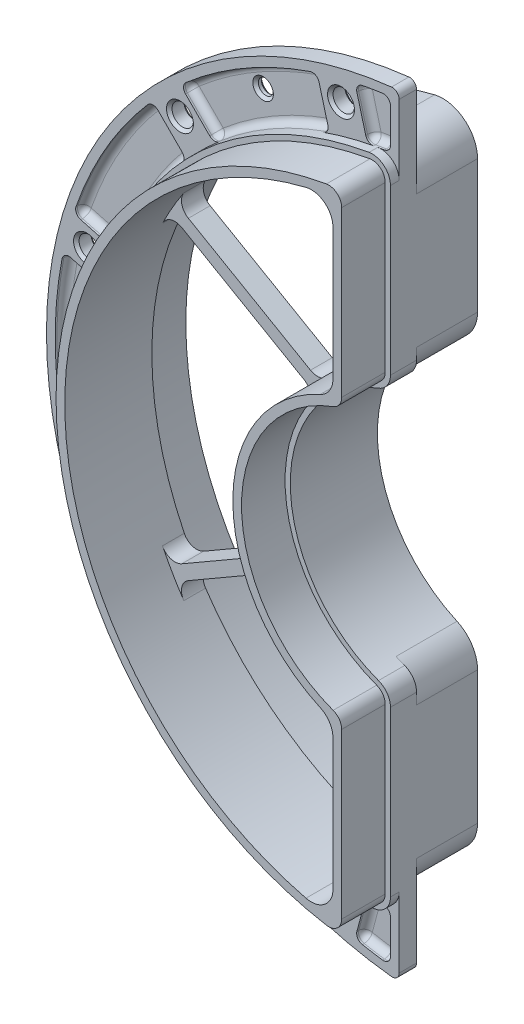
SolidWorks part; units mm, degrees
material "6061 Alloy"
ref_plane "Front" through (0, 0, 0) normal (0, 0, 1) x (1, 0, 0)
ref_plane "Top" through (0, 0, 0) normal (0, 1, 0) x (1, 0, 0)
ref_plane "Right" through (0, 0, 0) normal (1, 0, 0) x (0, 0, -1)
sketch "Sketch1" plane through (0, 0, 0) normal (0, 0, 1) x (1, 0, 0)
  line L0 (-8, 75.5778) -> (-8, 29.95)
  line L1 (0, 0) -> (0, 48.8788) construction
  line L2 (-8, -29.95) -> (-8, -75.5778)
  line L3 (0, 0) -> (58.2509, 0) construction
  arc A0 (-8, 75.5778) -> (-8, -75.5778) centre (0, 0) ccw
  arc A1 (-8, 29.95) -> (-8, -29.95) centre (0, 0) ccw
  dimension "D1" = 76
  dimension "D2" = 31
  dimension "D3" = 8
extrude "Extrude-Thin1" add sketch "Sketch1" along normal blind 16 thin
fillet "Fillet1" radius 5 4 edges at (-11.2, -71.9333, 8) (-11.2, -32.3141, 8) (-11.2, 32.3141, 8) (-11.2, 71.9333, 8)
fillet "Fillet2" radius 4.2 4 edges at (-8, 75.5778, 8) (-8, 29.95, 8) (-8, -29.95, 8) (-8, -75.5778, 8)
sketch "Sketch2" plane through (0, 0, 16) normal (0, 0, 1) x (1, 0, 0)
  line L0 (-8, 33.0182) -> (-8, 70.7559) construction
  line L1 (-8, -70.7559) -> (-8, -33.0182) construction
  line L2 (-8, 33.0182) -> (-8, 70.7559)
  line L3 (-8, -70.7559) -> (-8, -33.0182)
  arc A0 (-8, 70.7559) -> (-12.9136, 74.8948) centre (-12.2, 70.7559) ccw construction
  arc A1 (-12.9136, 74.8948) -> (-12.9136, -74.8948) centre (0, 0) ccw construction
  arc A2 (-12.9136, -74.8948) -> (-8, -70.7559) centre (-12.2, -70.7559) ccw construction
  arc A3 (-8, -33.0182) -> (-10.7443, -29.0785) centre (-12.2, -33.0182) ccw construction
  arc A4 (-10.7443, 29.0785) -> (-10.7443, -29.0785) centre (0, 0) ccw construction
  arc A5 (-10.7443, 29.0785) -> (-8, 33.0182) centre (-12.2, 33.0182) ccw construction
  arc A6 (-8, 70.7559) -> (-12.9136, 74.8948) centre (-12.2, 70.7559) ccw
  arc A7 (-12.9136, 74.8948) -> (-12.9136, -74.8948) centre (0, 0) ccw
  arc A8 (-12.9136, -74.8948) -> (-8, -70.7559) centre (-12.2, -70.7559) ccw
  arc A9 (-8, -33.0182) -> (-10.7443, -29.0785) centre (-12.2, -33.0182) ccw
  arc A10 (-10.7443, 29.0785) -> (-10.7443, -29.0785) centre (0, 0) ccw
  arc A11 (-10.7443, 29.0785) -> (-8, 33.0182) centre (-12.2, 33.0182) ccw
extrude "Cut-Extrude-Thin1" cut sketch "Sketch2" against normal blind 10 thin thin type one direction reverse wall 1.2
sketch "Sketch3" plane through (0, 0, 6) normal (0, 0, 1) x (1, 0, 0)
  line L0 (0, 0) -> (-22.1291, 0) construction
  line L4 (0, 0) -> (0, 34.7436) construction
  line L5 (-8, -70.7559) -> (-8, -33.0182) construction
  line L6 (-8, -70.7559) -> (-8, -88.6397)
  line L7 (-8, 70.7559) -> (-8, 88.6397)
  arc A0 (-8, 88.6397) -> (-8, -88.6397) centre (0, 0) ccw
  arc A1 (-12.9136, 74.8948) -> (-12.9136, -74.8948) centre (0, 0) ccw construction
  arc A2 (-8, 70.7559) -> (-12.9136, 74.8948) centre (-12.2, 70.7559) ccw construction
  arc A3 (-12.9136, -74.8948) -> (-8, -70.7559) centre (-12.2, -70.7559) ccw construction
  arc A4 (-12.9136, 74.8948) -> (-12.9136, -74.8948) centre (0, 0) ccw
  arc A5 (-8, 70.7559) -> (-12.9136, 74.8948) centre (-12.2, 70.7559) ccw
  arc A6 (-12.9136, -74.8948) -> (-8, -70.7559) centre (-12.2, -70.7559) ccw
  point P10 (-138.2875, 0)
  dimension "D3" = 178
extrude "Boss-Extrude1" add sketch "Sketch3" against normal blind 4 from offset 2 separate body offset against normal yes
sketch "Sketch9" plane through (0, 0, 4) normal (0, 0, 1) x (1, 0, 0)
  line L2 (-10, 70.7559) -> (-10, 88.6397)
  line L3 (-10, 75.3392) -> (-10, 86.4234)
  line L6 (-10, -88.6397) -> (-10, -70.7559)
  line L7 (-10, -86.4234) -> (-10, -75.3392)
  arc A2 (-12.9136, 74.8948) -> (-12.9136, -74.8948) centre (0, 0) ccw construction
  arc A3 (-7.8202, 86.6478) -> (-7.8202, -86.6478) centre (0, 0) ccw
  arc A4 (-10, 86.4234) -> (-10, -86.4234) centre (0, 0) ccw
  arc A5 (-10, 75.3392) -> (-10, -75.3392) centre (0, 0) ccw
  dimension "D1" = 2
  dimension "D2" = 2
  dimension "D3" = 2
extrude "Cut-Extrude2" cut sketch "Sketch9" against normal offset from surface (2 mm away) 2 up to face at (-33.3314, 0, 0)
sketch "Sketch10" plane through (0, 0, 4) normal (0, 0, 1) x (1, 0, 0)
  line L0 (0, 0) -> (-21.0938, -78.723) construction
  line L1 (-27.058, -83.5953) -> (-18.3647, -85.9247)
  line L2 (-18.3647, -85.9247) -> (-15.1295, -73.8506)
  line L3 (-15.1295, -73.8506) -> (-23.8228, -71.5212)
  line L4 (-23.8228, -71.5212) -> (-27.058, -83.5953)
  line L5 (-18.3647, -85.9247) -> (-23.8228, -71.5212) construction
  line L6 (0, 0) -> (0, -132.8188) construction
  point P5 (-21.0938, -78.723)
  dimension "D2" = 12.5
  dimension "D1" = 81.5
  dimension "D3" = 9
  dimension "D4" = 15
extrude "Boss-Extrude2" add sketch "Sketch10" against normal up to surface (2 mm away) up to face at (-34.3197, 0, 2)
pattern_circular "CirPattern1" count 6 over 150 about axis through (0, 0, 0) along (0, 0, 1) of "Boss-Extrude2"
sketch "Sketch11" plane through (0, 0, 4) normal (0, 0, 1) x (1, 0, 0)
  line L0 (0, 0) -> (0, -70.2998) construction
  line L1 (0, 0) -> (-21.3526, -79.6889) construction
  line L2 (0, 0) -> (-58.3363, -58.3363) construction
  point P4 (-21.3526, -79.6889)
  point P8 (-58.3363, -58.3363)
  point P9 (-79.6889, -21.3526)
  point P10 (-79.6889, 21.3526)
  point P11 (-58.3363, 58.3363)
  point P12 (-21.3526, 79.6889)
  dimension "D2" = 30
  dimension "D3" = 15
  dimension "D4" = 82.5
  dimension "D1" = 6
hole_wizard "#8 Clearance Hole1" positions "3DSketch1" profile "Sketch12" hole size "#8" standard "Ansi Inch" end condition through all
sketch3d "3DSketch1"
  point P0 (-21.3526, -79.6889, 4)
  point P3 (-58.3363, -58.3363, 4)
  point P6 (-79.6889, -21.3526, 4)
  point P9 (-79.6889, 21.3526, 4)
  point P12 (-58.3363, 58.3363, 4)
  point P15 (-21.3526, 79.6889, 4)
sketch "Sketch12" plane through (-21.3526, -79.6889, 4) normal (1, 0, 0) x (0, -1, 0)
  line L0 (0, 0) -> (0, 4)
  line L1 (0, 4) -> (3.0924, 4)
  line L2 (2.4574, 3.365) -> (2.4574, 0.635)
  line L3 (2.4574, 0.635) -> (3.0924, 0)
  line L5 (3.0924, 0) -> (0, 0)
  line L6 (-2.4574, 0.635) -> (-3.0924, 0) construction
  line L7 (3.0924, 4) -> (2.4574, 3.365)
  line L8 (-3.0925, 4) -> (-2.4574, 3.365) construction
  line L11 (0, -6.35) -> (0, 107.95) construction
  dimension "Thru Hole Dia." = 4.9149
  dimension "Thru Hole Depth" = 4
  dimension "Near C'Sink Dia." = 6.1849
  dimension "Near C'Sink Angle" = 90
  dimension "Far C'Sink Dia." = 6.1849
  dimension "Far C'Sink Angle" = 90
fillet "Fillet3" radius 1.5875 56 edges at (-10, -80.8813, 2) (-14.0861, -85.8521, 2) (-16.7148, -79.767, 2) (-12.6524, -74.9394, 2) (-10, -86.4234, 3) (-10, -75.3392, 3) (-18.1404, -85.0877, 3) (-15.2891, -74.4463, 3) (-14.0861, 85.8521, 2) (-10, 80.8813, 2) (-12.6524, 74.9394, 2) (-16.7148, 79.767, 2) (-38, 65.8179, 2) (-54.3589, 60.7229, 2) (-43.5, 75.3442, 2) (-25.4081, 77.4376, 2) (-65.8179, 38, 2) (-77.4376, 25.4081, 2) (-75.3442, 43.5, 2) (-60.7229, 54.3589, 2) (-76, 0, 2) (-79.767, -16.7148, 2) (-87, 0, 2) (-79.767, 16.7148, 2) (-65.8179, -38, 2) (-60.7229, -54.3589, 2) (-75.3442, -43.5, 2) (-77.4376, -25.4081, 2) (-38, -65.8179, 2) (-25.4081, -77.4376, 2) (-43.5, -75.3442, 2) (-54.3589, -60.7229, 2) (-18.1404, 85.0877, 3) (-10, 86.4234, 3) (-15.2891, 74.4463, 3) (-10, 75.3392, 3) (-26.8338, 82.7584, 3) (-23.9824, 72.1169, 3) (-58.254, 64.6179, 3) (-50.4638, 56.8278, 3) (-82.7584, 26.8338, 3) (-64.6179, 58.254, 3) (-56.8278, 50.4638, 3) (-72.1169, 23.9824, 3) (-85.0877, 18.1404, 3) (-74.4463, 15.2891, 3) (-85.0877, -18.1404, 3) (-74.4463, -15.2891, 3) (-82.7584, -26.8338, 3) (-72.1169, -23.9824, 3) (-56.8278, -50.4638, 3) (-64.6179, -58.254, 3) (-50.4638, -56.8278, 3) (-58.254, -64.6179, 3) (-26.8338, -82.7584, 3) (-23.9824, -72.1169, 3)
fillet "Fillet4" radius 1.5875 2 edges at (-8, -88.6397, 2) (-8, 88.6397, 2)
sketch "Sketch8" plane through (0, 0, 0) normal (0, 1, 0) x (1, 0, 0)
  line L1 (-129.2875, -26.448) -> (-129.2875, -58.4649)
sketch "Sketch17" plane through (0, 0, 0) normal (0, 0, -1) x (-1, 0, 0)
  line L0 (8, 75.5778) -> (8, 29.95) construction
  line L1 (8, -29.95) -> (8, -75.5778) construction
  line L2 (8, 75.5778) -> (8, 29.95)
  line L3 (8, -29.95) -> (8, -75.5778)
  arc A0 (8, -29.95) -> (8, 29.95) centre (0, 0) ccw construction
  arc A1 (8, -75.5778) -> (8, 75.5778) centre (0, 0) ccw construction
  arc A2 (8, -29.95) -> (8, 29.95) centre (0, 0) ccw
  arc A3 (8, -75.5778) -> (8, 75.5778) centre (0, 0) ccw
extrude "Extrude-Thin2" add sketch "Sketch17" along normal blind 14 separate body thin thin type one direction reverse wall 3.2
fillet "Fillet5" radius 5 4 edges at (-11.2, 71.9333, -7) (-11.2, -71.9333, -7) (-11.2, -32.3141, -7) (-11.2, 32.3141, -7)
fillet "Fillet6" radius 8 4 edges at (-8, 29.95, -7) (-8, -29.95, -7) (-8, -75.5778, -7) (-8, 75.5778, -7)
combine bodies "Combine1" operation type add bodies to combine 113 117
sketch "Sketch7" plane through (0, 0, -14) normal (0, 0, -1) x (-1, 0, 0)
  line L4 (9, 66.0908) -> (9, 35.5668)
  line L5 (9, -35.5668) -> (9, -66.0908)
  line L6 (9, 66.0908) -> (9, 35.5668)
  line L7 (9, -35.5668) -> (9, -66.0908)
  arc A12 (17.6471, 72.8943) -> (9, 66.0908) centre (16, 66.0908) ccw
  arc A13 (9, 35.5668) -> (13.1282, 29.183) centre (16, 35.5668) ccw
  arc A14 (13.1282, -29.183) -> (13.1282, 29.183) centre (0, 0) ccw
  arc A15 (13.1282, -29.183) -> (9, -35.5668) centre (16, -35.5668) ccw
  arc A16 (9, -66.0908) -> (17.6471, -72.8943) centre (16, -66.0908) ccw
  arc A17 (17.6471, -72.8943) -> (17.6471, 72.8943) centre (0, 0) ccw
  arc A18 (17.6471, 72.8943) -> (9, 66.0908) centre (16, 66.0908) ccw
  arc A19 (9, 35.5668) -> (13.1282, 29.183) centre (16, 35.5668) ccw
  arc A20 (13.1282, -29.183) -> (13.1282, 29.183) centre (0, 0) ccw
  arc A21 (13.1282, -29.183) -> (9, -35.5668) centre (16, -35.5668) ccw
  arc A22 (9, -66.0908) -> (17.6471, -72.8943) centre (16, -66.0908) ccw
  arc A23 (17.6471, -72.8943) -> (17.6471, 72.8943) centre (0, 0) ccw
  dimension "D1" = 1
extrude "Cut-Extrude1" cut sketch "Sketch7" against normal blind 10
sketch "Sketch13" plane through (0, 0, 2) normal (0, 0, 1) x (1, 0, 0)
  line L0 (0, 0) -> (0, -89.236) construction
  line L1 (0, -89.236) -> (0, 0) construction
  line L2 (0, 0) -> (-41.25, -71.4471) construction
  dimension "D1" = 30
  dimension "D2" = 82.5
hole_wizard "#29 (0.136) Diameter Hole1" positions "Sketch15" profile "Sketch14" hole size "#29" standard "Ansi Inch" end condition up to next
sketch "Sketch15" plane through (0, 0, 2) normal (0, 0, 1) x (1, 0, 0)
  point P0 (-41.25, -71.4471)
sketch "Sketch14" plane through (-41.25, -71.4471, 2) normal (1, 0, 0) x (0, -1, 0)
  line L0 (0, 0) -> (0, 2)
  line L1 (0, 2) -> (2.3622, 2)
  line L2 (1.7272, 1.365) -> (1.7272, 0.635)
  line L3 (1.7272, 0.635) -> (2.3622, 0)
  line L5 (2.3622, 0) -> (0, 0)
  line L6 (-1.7272, 0.635) -> (-2.3622, 0) construction
  line L7 (2.3622, 2) -> (1.7272, 1.365)
  line L8 (-2.3622, 2) -> (-1.7272, 1.365) construction
  line L11 (0, -6.35) -> (0, 107.95) construction
  dimension "Thru Hole Dia." = 3.4544
  dimension "Thru Hole Depth" = 2
  dimension "Near C'Sink Dia." = 4.7244
  dimension "Near C'Sink Angle" = 90
  dimension "Far C'Sink Dia." = 4.7244
  dimension "Far C'Sink Angle" = 90
mirror "Mirror1" about plane through (0, 0, 0) normal (0, 1, 0) of "#29 (0.136) Diameter Hole1"
sketch "Sketch18" plane through (0, 0, -4) normal (0, 0, 1) x (1, 0, 0)
  line L0 (0, 0) -> (-81.2105, -46.8869) construction
  line L1 (0, 0) -> (-53.5103, 0) construction
  line L2 (-62.2833, -37.6913) -> (-28.8396, -18.3826)
  line L3 (-63.7833, -35.0932) -> (-30.3396, -15.7845)
  arc A0 (-17.3947, 70.6913) -> (-17.3947, -70.6913) centre (0, 0) ccw construction
  arc A1 (-14.1337, 31.1429) -> (-14.1337, -31.1429) centre (0, 0) ccw construction
  arc A2 (-63.7833, -35.0932) -> (-62.2833, -37.6913) centre (0, 0) ccw
  arc A4 (-30.3396, -15.7845) -> (-28.8396, -18.3826) centre (0, 0) ccw
  dimension "D1" = 30
  dimension "D2" = 3
extrude "Boss-Extrude3" add sketch "Sketch18" along normal blind 5
mirror "Mirror2" about plane through (0, 0, 0) normal (0, 1, 0) of "Boss-Extrude3"
fillet "Fillet7" radius 3.175 8 edges at (-63.7833, -35.0932, -1.5) (-30.3396, -15.7845, -1.5) (-28.8396, -18.3826, -1.5) (-62.2833, -37.6913, -1.5) (-62.2833, 37.6913, -1.5) (-28.8396, 18.3826, -1.5) (-30.3396, 15.7845, -1.5) (-63.7833, 35.0932, -1.5)
